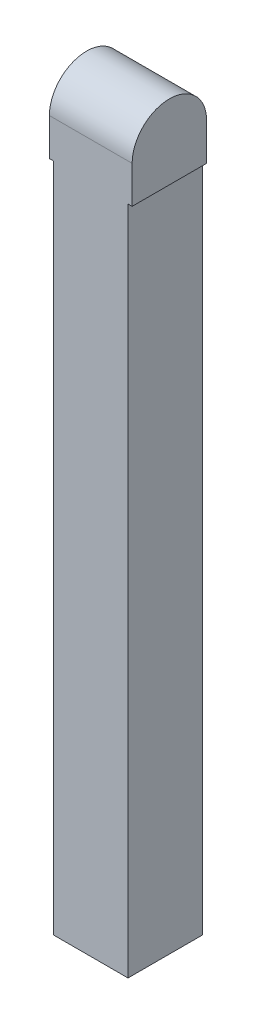
SolidWorks part; units mm, degrees
ref_plane "Front" through (0, 0, 0) normal (0, 0, 1) x (1, 0, 0)
ref_plane "Top" through (0, 0, 0) normal (0, 1, 0) x (1, 0, 0)
ref_plane "Right" through (0, 0, 0) normal (1, 0, 0) x (0, 0, -1)
sketch "草图1" plane through (0, 0, 0) normal (0, 1, 0) x (1, 0, 0)
  line L0 (-16.0588, 0) -> (0, 0) construction
  line L1 (0, 0) -> (0, 20.7206) construction
  line L3 (-9, 9) -> (9, 9)
  line L4 (-9, 9) -> (-9, -9)
  line L5 (-9, -9) -> (9, -9)
  line L6 (9, 9) -> (9, -9)
  dimension "D1" = 18
  dimension "D2" = 9
  dimension "D4" = 18
  dimension "D5" = 9
extrude "凸台-拉伸1" add sketch "草图1" along normal blind 160
sketch "草图2" plane through (0, 160, 0) normal (0, 1, 0) x (1, 0, 0)
  line L1 (-9, 9) -> (9, 9)
  line L2 (-9, 9) -> (-9, -9)
  line L3 (-9, -9) -> (9, -9)
  line L4 (9, 9) -> (9, -9)
extrude "凸台-拉伸2" add sketch "草图2" along normal blind 2
sketch "草图3" plane through (0, 162, 0) normal (0, 1, 0) x (1, 0, 0)
  line L13 (-10, 9) -> (10, 9)
  line L14 (-10, 9) -> (-10, -9)
  line L15 (-10, -9) -> (10, -9)
  line L16 (10, 9) -> (10, -9)
  dimension "D1" = 18
  dimension "D2" = 20
  dimension "D3" = 10
extrude "凸台-拉伸4" add sketch "草图3" along normal blind 18
sketch "草图4" plane through (-10, 0, 0) normal (-1, 0, 0) x (0, 0, 1)
  line L0 (-9, 180) -> (9, 180) construction
  line L2 (-9, 171) -> (-9, 185)
  line L3 (-9, 185) -> (9, 185)
  line L4 (9, 171) -> (9, 185)
  arc A0 (9, 171) -> (-9, 171) centre (0, 171) ccw
  dimension "D1" = 5
  dimension "D2" = 9
extrude "切除-拉伸1" cut sketch "草图4" against normal through all
